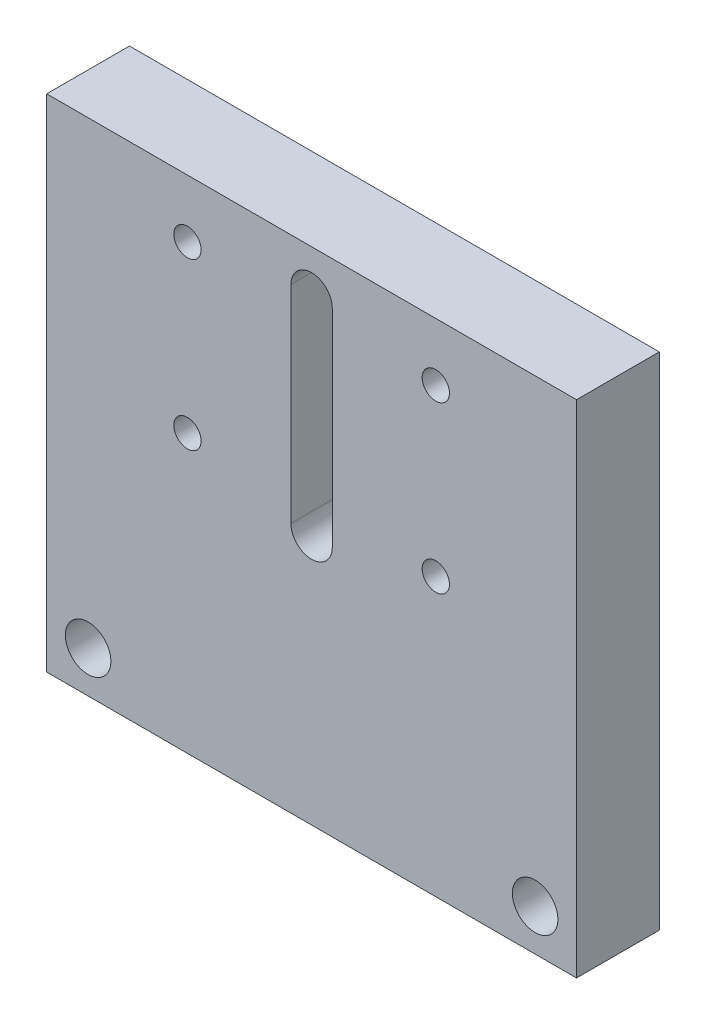
SolidWorks part; units mm, degrees
ref_plane "Front Plane" through (0, 0, 0) normal (0, 0, 1) x (1, 0, 0)
ref_plane "Top Plane" through (0, 0, 0) normal (0, 1, 0) x (1, 0, 0)
ref_plane "Right Plane" through (0, 0, 0) normal (1, 0, 0) x (0, 0, -1)
sketch "Sketch1" plane through (0, 0, 0) normal (1, 0, 0) x (0, 0, -1)
  line L0 (0, 60.5) -> (0, 0)
  line L1 (0, 0) -> (98, 0)
  line L2 (98, 0) -> (98, 10)
  line L3 (98, 10) -> (10, 10)
  line L4 (10, 10) -> (10, 60.5)
  line L5 (10, 60.5) -> (0, 60.5)
  dimension "D1" = 98
  dimension "D2" = 10
  dimension "D3" = 10
  dimension "D4" = 60.5
extrude "Boss-Extrude1" add sketch "Sketch1" along normal blind 64
ref_plane "Plane1" through (32, 0, 0) normal (-1, 0, 0) x (0, 0, 1)
sketch "Sketch3" plane through (0, 0, -10) normal (0, 0, -1) x (-1, 0, 0)
  line L0 (-64, 60.5) -> (0, 60.5) construction
  line L1 (-32, -4.4) -> (-32, 4.4) construction
  circle A0 centre (-47, 53.5) radius 2.25
  dimension "D1" = 7
  dimension "D3" = 4.5
  dimension "D2" = 15
extrude "Cut-Extrude1" [suppressed] cut sketch "Sketch3" against normal up to next
pattern_linear "LPattern1" [suppressed] count 2 spacing 30 count 2 spacing 20
sketch "Sketch4" plane through (0, 10, 0) normal (0, 1, 0) x (1, 0, 0)
  line L0 (64, 98) -> (0, 98) construction
  line L1 (64, 98) -> (64, 10) construction
  circle A0 centre (60.25, 89) radius 2.25
  dimension "D1" = 4.5
  dimension "D2" = 9
  dimension "D3" = 3.75
extrude "Cut-Extrude2" cut sketch "Sketch4" against normal up to next (10 mm away)
pattern_linear "LPattern2" count 2 spacing 12 along (0, 0, 1) count 2 spacing 56.5 along (-1, 0, 0) of "Cut-Extrude2"
sketch "Sketch5" plane through (0, 0, -10) normal (0, 0, -1) x (-1, 0, 0)
  line L0 (-32, 55.3) -> (-32, 30.3) construction
  line L1 (-32, -4.4) -> (-32, 4.4) construction
  line L2 (-29.5, 55.3) -> (-29.5, 30.3)
  line L3 (-34.5, 55.3) -> (-34.5, 30.3)
  line L4 (-64, 60.5) -> (0, 60.5) construction
  arc A0 (-29.5, 55.3) -> (-34.5, 55.3) centre (-32, 55.3) ccw
  arc A1 (-34.5, 30.3) -> (-29.5, 30.3) centre (-32, 30.3) ccw
  point P4 (-32, 42.8)
  dimension "D2" = 2.5
  dimension "D3" = 25
  dimension "D1" = 5.2
extrude "Cut-Extrude3" cut sketch "Sketch5" against normal blind 10
sketch "Sketch6" plane through (0, 10, 0) normal (0, 1, 0) x (1, 0, 0)
  line L0 (64, 98) -> (0, 98) construction
  line L1 (64, 98) -> (64, 10) construction
  circle A0 centre (38, 94.1) radius 2.75
  dimension "D1" = 5.5
  dimension "D2" = 3.9
  dimension "D3" = 26
extrude "Cut-Extrude4" cut sketch "Sketch6" against normal blind 1.5
pattern_linear "LPattern3" count 2 spacing 12 along (-1, 0, 0) count 2 spacing 22.2 along (0, 0, 1) of "Cut-Extrude4"
chamfer "Chamfer1" [suppressed] distance 0.5 angle 45
sketch "Sketch7" plane through (64, 0, 0) normal (1, 0, 0) x (0, 0, -1)
  line L1 (10, 60.5) -> (103.832, 60.5)
  line L2 (10, 60.5) -> (10, -4.2572)
  line L3 (10, -4.2572) -> (103.832, -4.2572)
  line L4 (103.832, 60.5) -> (103.832, -4.2572)
extrude "Cut-Extrude5" cut sketch "Sketch7" against normal through all
sketch "Sketch8" plane through (0, 0, 0) normal (0, 0, 1) x (1, 0, 0)
  line L0 (64, 0) -> (0, 0) construction
  line L1 (64, 60.5) -> (64, 0) construction
  circle A0 centre (59, 5) radius 2.75
  dimension "D1" = 5.5
  dimension "D2" = 5
  dimension "D3" = 5
extrude "Cut-Extrude6" cut sketch "Sketch8" against normal through all
mirror "Mirror1" about plane through (32, 0, 0) normal (-1, 0, 0) of "Cut-Extrude6"
hole_wizard "M4 Tapped Hole1" positions "Sketch10" profile "Sketch9" tap size "M4" standard "ISO" end condition through all
sketch "Sketch10" plane through (0, 0, -10) normal (0, 0, -1) x (-1, 0, 0)
  line L1 (-32, -4.4) -> (-32, 4.4) construction
  point P2 (-17, 53.5)
  point P18 (-47, 33.5)
  point P21 (-17, 33.5)
  point P25 (-47, 53.5)
  dimension "D1" = 15
sketch "Sketch9" plane through (17, 53.5, -10) normal (1, 0, 0) x (0, 1, 0)
  line L0 (0, 0) -> (0, 10)
  line L1 (0, 10) -> (1.65, 10)
  line L2 (1.65, 10) -> (1.65, 0)
  line L5 (1.65, 0) -> (0, 0)
  line L11 (0, -6.35) -> (0, 107.95) construction
  dimension "Thru Tap Drill Dia." = 3.3
  dimension "Thru Tap Drill Depth" = 10
cosmetic thread "Hole Thread5" parameters "D1"=10, "D2"=4
cosmetic thread "Hole Thread6" parameters "D1"=10, "D2"=4
cosmetic thread "Hole Thread7" parameters "D1"=10, "D2"=4
cosmetic thread "Hole Thread8" parameters "D1"=10, "D2"=4
